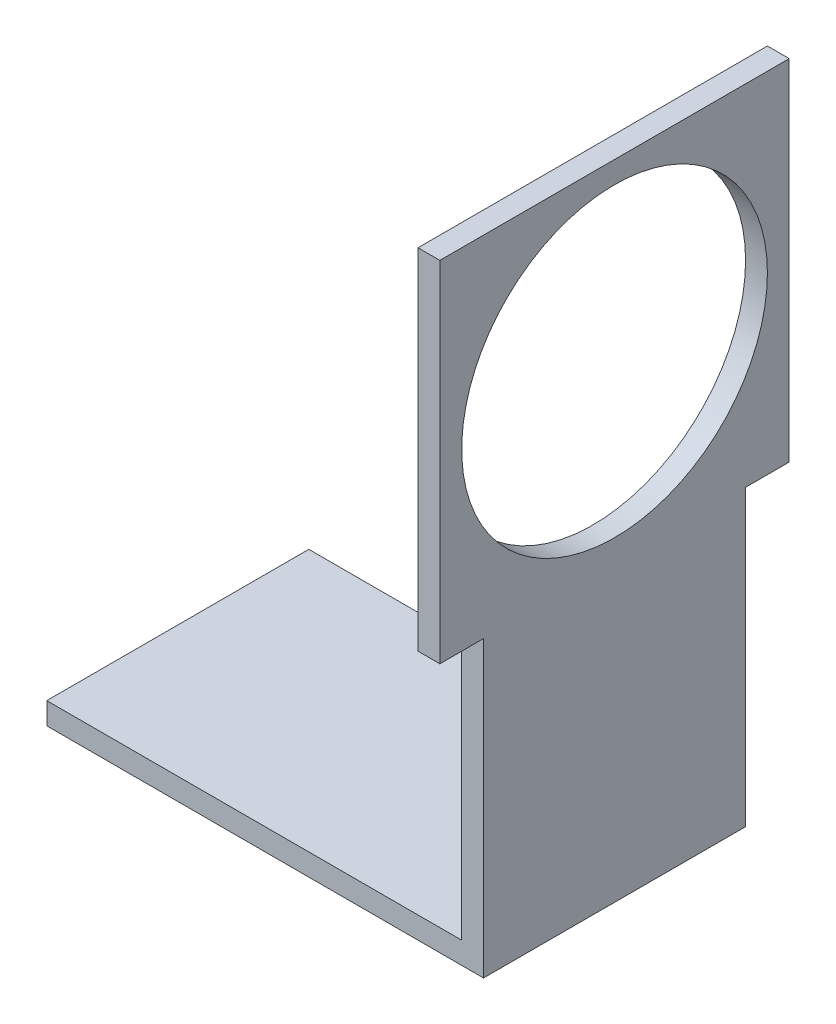
SolidWorks part; units mm, degrees
ref_plane "Front Plane" through (0, 0, 0) normal (0, 0, 1) x (1, 0, 0)
ref_plane "Top Plane" through (0, 0, 0) normal (0, 1, 0) x (1, 0, 0)
ref_plane "Right Plane" through (0, 0, 0) normal (1, 0, 0) x (0, 0, -1)
sketch "Sketch1" plane through (0, 0, 0) normal (0, 1, 0) x (1, 0, 0)
  line L1 (-93.0573, 30.7643) -> (6.9427, 30.7643)
  line L2 (-93.0573, 30.7643) -> (-93.0573, -29.2357)
  line L3 (-93.0573, -29.2357) -> (6.9427, -29.2357)
  line L4 (6.9427, 30.7643) -> (6.9427, -29.2357)
  dimension "D1" = 60
  dimension "D2" = 100
extrude "Boss-Extrude1" add sketch "Sketch1" along normal blind 5
sketch "Sketch2" plane through (0, 5, 0) normal (0, 1, 0) x (1, 0, 0)
  line L0 (-93.0573, -29.2357) -> (6.9427, -29.2357) construction
  line L1 (6.9427, 30.7643) -> (1.9427, 30.7643)
  line L2 (6.9427, 30.7643) -> (6.9427, -29.2357)
  line L3 (6.9427, -29.2357) -> (1.9427, -29.2357)
  line L4 (1.9427, 30.7643) -> (1.9427, -29.2357)
  dimension "D1" = 5
extrude "Boss-Extrude2" add sketch "Sketch2" along normal blind 62.3
sketch "Sketch4" plane through (6.9427, 0, 0) normal (1, 0, 0) x (0, 0, -1)
  line L0 (-29.2357, 67.3) -> (40.7643, 67.3)
  line L1 (40.7643, 67.3) -> (40.7643, 147.3)
  line L2 (40.7643, 147.3) -> (-39.2357, 147.3)
  line L3 (-39.2357, 147.3) -> (-39.2357, 67.3)
  line L4 (-39.2357, 67.3) -> (-29.2357, 67.3)
  line L5 (30.7643, 67.3) -> (30.7643, 0) construction
  dimension "D1" = 10
  dimension "D2" = 10
  dimension "D3" = 80
extrude "Boss-Extrude3" add sketch "Sketch4" against normal blind 5
sketch "Sketch5" plane through (6.9427, 0, 0) normal (1, 0, 0) x (0, 0, -1)
  line L0 (40.7643, 147.3) -> (-39.2357, 147.3) construction
  circle A0 centre (0.7643, 107.3) radius 35
  dimension "D1" = 70
  dimension "D2" = 40
extrude "Cut-Extrude1" cut sketch "Sketch5" against normal blind 5
